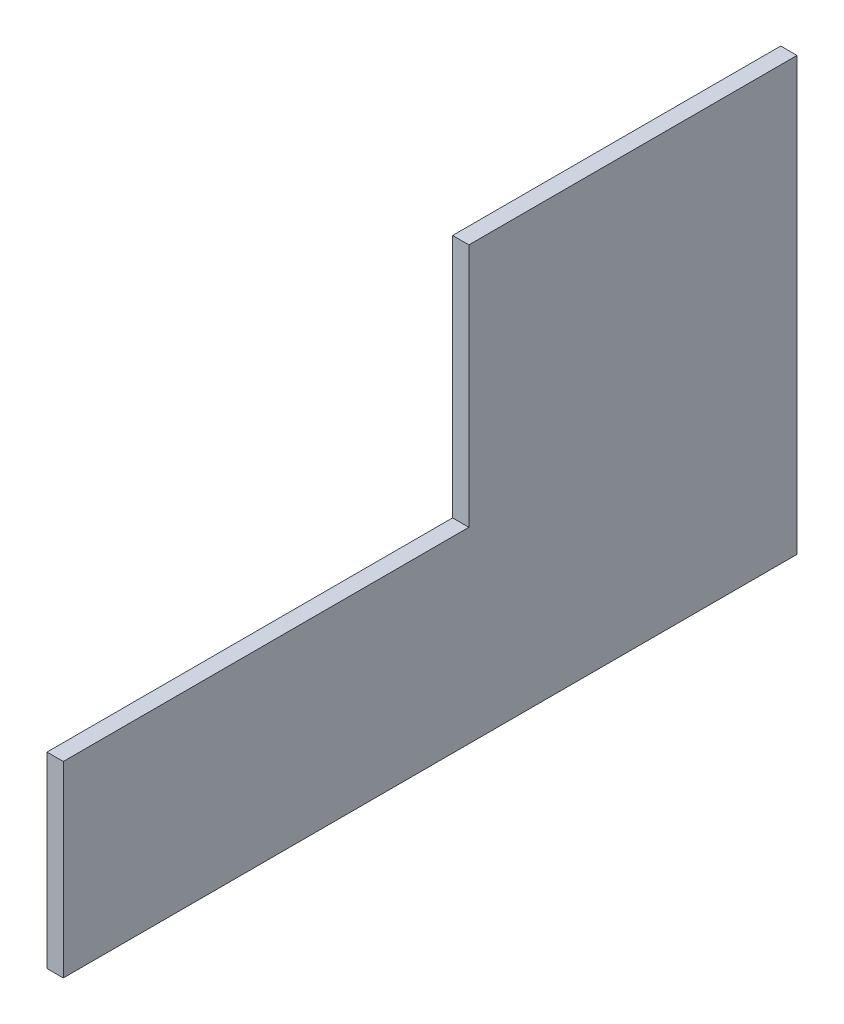
SolidWorks part; units mm, degrees
ref_plane "Front Plane" through (0, 0, 0) normal (0, 0, 1) x (1, 0, 0)
ref_plane "Top Plane" through (0, 0, 0) normal (0, 1, 0) x (1, 0, 0)
ref_plane "Right Plane" through (0, 0, 0) normal (1, 0, 0) x (0, 0, -1)
sketch "Sketch1" plane through (0, 0, 0) normal (1, 0, 0) x (0, 0, -1)
  line L1 (-90, 53) -> (90, 53)
  line L2 (-90, 53) -> (-90, -53)
  line L3 (-90, -53) -> (90, -53)
  line L4 (90, 53) -> (90, -53)
  line L5 (-90, 53) -> (90, -53) construction
  line L6 (-90, -53) -> (90, 53) construction
  line L11 (-90, 53) -> (9.5, 53)
  line L12 (-90, 53) -> (-90, -7)
  line L13 (-90, -7) -> (9.5, -7)
  line L14 (9.5, 53) -> (9.5, -7)
  line L21 (82, 0) -> (90, 0) construction
  line L22 (90, 53) -> (82, 53)
  line L23 (90, 53) -> (90, -53)
  line L24 (90, -53) -> (82, -53)
  line L25 (82, 53) -> (82, -53)
  line L27 (-82, -30) -> (-90, -30) construction
  line L28 (-90, -7) -> (-82, -7)
  line L29 (-90, -7) -> (-90, -53)
  line L30 (-90, -53) -> (-82, -53)
  line L31 (-82, -7) -> (-82, -53)
  point P0 (0, 0)
  point P42 (-82, -30)
  dimension "D1" = 106
  dimension "D2" = 180
  dimension "D3" = 99.5
  dimension "D4" = 60
  dimension "D9" = 8
  dimension "D13" = 8
extrude "Boss-Extrude1" add sketch "Sketch1" against normal blind 4
